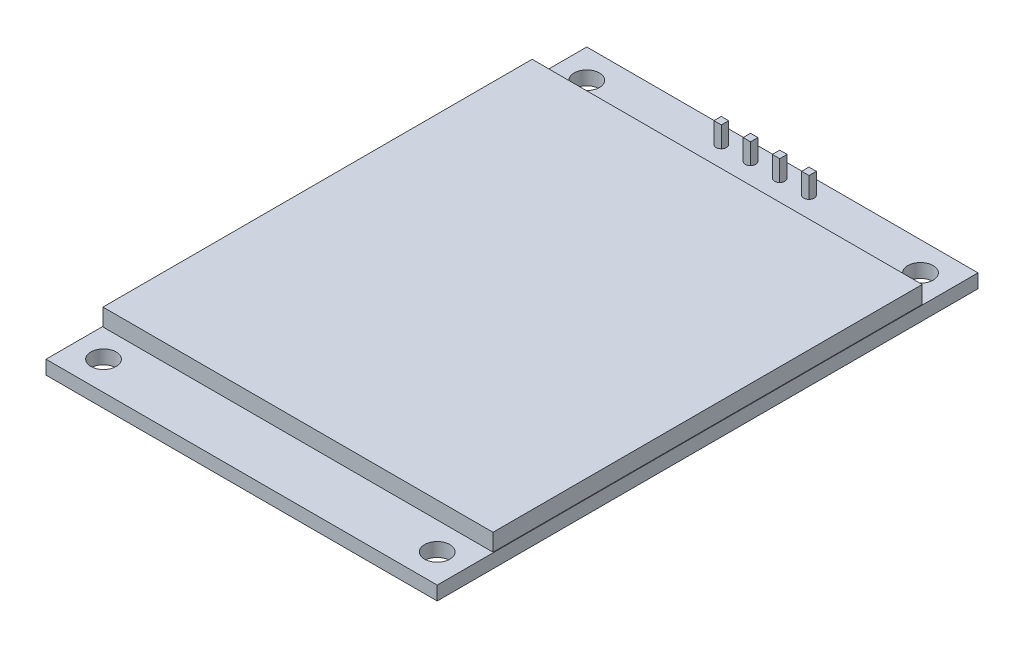
SolidWorks part; units mm, degrees
ref_plane "Front Plane" through (0, 0, 0) normal (0, 0, 1) x (1, 0, 0)
ref_plane "Top Plane" through (0, 0, 0) normal (0, 1, 0) x (1, 0, 0)
ref_plane "Right Plane" through (0, 0, 0) normal (1, 0, 0) x (0, 0, -1)
sketch "Sketch1" plane through (0, 0, 0) normal (0, 1, 0) x (1, 0, 0)
  line L1 (17, -23.5) -> (-17, -23.5)
  line L2 (17, -23.5) -> (17, 23.5)
  line L3 (17, 23.5) -> (-17, 23.5)
  line L4 (-17, -23.5) -> (-17, 23.5)
  line L5 (17, -23.5) -> (-17, 23.5) construction
  line L6 (17, 23.5) -> (-17, -23.5) construction
  point P0 (0, 0)
  dimension "D1" = 34
  dimension "D2" = 47
extrude "Boss-Extrude1" add sketch "Sketch1" along normal mid plane 1.2
sketch "Sketch2" plane through (0, 0.6, 0) normal (0, 1, 0) x (1, 0, 0)
  line L1 (14.5, -21) -> (-14.5, -21) construction
  line L2 (14.5, -21) -> (14.5, 21) construction
  line L3 (14.5, 21) -> (-14.5, 21) construction
  line L4 (-14.5, -21) -> (-14.5, 21) construction
  line L5 (14.5, -21) -> (-14.5, 21) construction
  line L6 (14.5, 21) -> (-14.5, -21) construction
  circle A0 centre (-14.5, 21) radius 1.1
  circle A1 centre (14.5, 21) radius 1.1
  circle A2 centre (14.5, -21) radius 1.1
  circle A3 centre (-14.5, -21) radius 1.1
  point P0 (0, 0)
  dimension "D3" = 2.2
  dimension "D1" = 42
  dimension "D2" = 29
extrude "Cut-Extrude1" cut sketch "Sketch2" against normal through all
sketch "Sketch3" plane through (0, 0.6, 0) normal (0, 1, 0) x (1, 0, 0)
  line L0 (-3.81, 22) -> (3.81, 22) construction
  line L1 (17, 23.5) -> (-17, 23.5) construction
  circle A0 centre (-3.81, 22) radius 0.45
  circle A1 centre (-1.27, 22) radius 0.45
  circle A2 centre (1.27, 22) radius 0.45
  circle A3 centre (3.81, 22) radius 0.45
  point P13 (0, 22)
  dimension "D5" = 0.9
  dimension "D1" = 2.54
  dimension "D2" = 2.54
  dimension "D3" = 2.54
  dimension "D4" = 1.5
extrude "Cut-Extrude2" cut sketch "Sketch3" against normal through all
sketch "Sketch4" plane through (0, -0.6, 0) normal (0, -1, 0) x (1, 0, 0)
  line L0 (-1.27, -22) -> (1.27, -22) construction
  line L1 (5.08, -23.27) -> (-5.08, -23.27)
  line L2 (5.08, -23.27) -> (5.08, -20.73)
  line L3 (5.08, -20.73) -> (-5.08, -20.73)
  line L4 (-5.08, -23.27) -> (-5.08, -20.73)
  line L5 (5.08, -23.27) -> (-5.08, -20.73) construction
  line L6 (5.08, -20.73) -> (-5.08, -23.27) construction
  circle A0 centre (3.81, -22) radius 0.45 construction
  circle A1 centre (1.27, -22) radius 0.45 construction
  circle A2 centre (-1.27, -22) radius 0.45 construction
  circle A3 centre (-3.81, -22) radius 0.45 construction
  circle A4 centre (3.81, -22) radius 0.45
  circle A5 centre (1.27, -22) radius 0.45
  circle A6 centre (-1.27, -22) radius 0.45
  circle A7 centre (-3.81, -22) radius 0.45
  point P0 (0, -22)
  dimension "D1" = 2.54
  dimension "D2" = 10.16
extrude "Boss-Extrude2" add sketch "Sketch4" along normal blind 2.54 separate body
sketch "Sketch5" plane through (0, 0.6, 0) normal (0, 1, 0) x (1, 0, 0)
  line L0 (-1.59, 22.32) -> (-1.59, 21.68)
  line L1 (-4.13, 22.32) -> (-3.49, 22.32)
  line L2 (-4.13, 22.32) -> (-4.13, 21.68)
  line L3 (-4.13, 21.68) -> (-3.49, 21.68)
  line L4 (-3.49, 22.32) -> (-3.49, 21.68)
  line L5 (-4.13, 22.32) -> (-3.49, 21.68) construction
  line L6 (-4.13, 21.68) -> (-3.49, 22.32) construction
  line L7 (-1.59, 22.32) -> (-0.95, 22.32)
  line L8 (-0.95, 22.32) -> (-0.95, 21.68)
  line L9 (-1.59, 21.68) -> (-0.95, 21.68)
  line L10 (0.95, 22.32) -> (0.95, 21.68)
  line L11 (0.95, 22.32) -> (1.59, 22.32)
  line L12 (1.59, 22.32) -> (1.59, 21.68)
  line L13 (0.95, 21.68) -> (1.59, 21.68)
  line L14 (3.49, 22.32) -> (3.49, 21.68)
  line L15 (3.49, 22.32) -> (4.13, 22.32)
  line L16 (4.13, 22.32) -> (4.13, 21.68)
  line L17 (3.49, 21.68) -> (4.13, 21.68)
  point P0 (-3.81, 22)
  dimension "D1" = 0.64
  dimension "D3" = 2.54
  dimension "D2" = 4
extrude "Boss-Extrude3" add sketch "Sketch5" against normal blind 11.3 from offset 1.8 separate body
sketch "Sketch6" plane through (0, 0.6, 0) normal (0, 1, 0) x (1, 0, 0)
  line L0 (17, 23.5) -> (-17, 23.5) construction
  line L1 (16.95, 18.7) -> (-16.95, 18.7)
  line L2 (16.95, 18.7) -> (16.95, -18.6)
  line L3 (16.95, -18.6) -> (-16.95, -18.6)
  line L4 (-16.95, 18.7) -> (-16.95, -18.6)
  line L5 (16.95, 18.7) -> (-16.95, -18.6) construction
  line L6 (16.95, -18.6) -> (-16.95, 18.7) construction
  point P0 (0, 0.05)
  dimension "D1" = 37.3
  dimension "D2" = 4.8
  dimension "D3" = 33.9
extrude "Boss-Extrude4" add sketch "Sketch6" along normal blind 1.5 separate body
sketch "Sketch7" plane through (0, 2.1, 0) normal (0, 1, 0) x (1, 0, 0)
  line L0 (16.95, 18.7) -> (-16.95, 18.7) construction
  line L1 (14.43, 17.3) -> (-14.43, 17.3)
  line L2 (14.43, 17.3) -> (14.43, -11.56)
  line L3 (14.43, -11.56) -> (-14.43, -11.56)
  line L4 (-14.43, 17.3) -> (-14.43, -11.56)
  line L5 (14.43, 17.3) -> (-14.43, -11.56) construction
  line L6 (14.43, -11.56) -> (-14.43, 17.3) construction
  line L8 (13.43, -10.56) -> (-13.43, -10.56)
  line L9 (13.43, -10.56) -> (13.43, 16.3)
  line L10 (13.43, 16.3) -> (-13.43, 16.3)
  line L11 (-13.43, -10.56) -> (-13.43, 16.3)
  line L12 (13.43, -10.56) -> (-13.43, 16.3) construction
  line L13 (13.43, 16.3) -> (-13.43, -10.56) construction
  point P0 (0, 2.87)
  point P7 (0, 0)
  point P9 (0, 2.87)
  dimension "D1" = 28.86
  dimension "D2" = 1.4
  dimension "D3" = 28.86
  dimension "D4" = 2.4
  dimension "D5" = 26.86
  dimension "D6" = 26.86
extrude "Boss-Extrude5" [suppressed] add sketch "Sketch7" along normal blind 0.1
